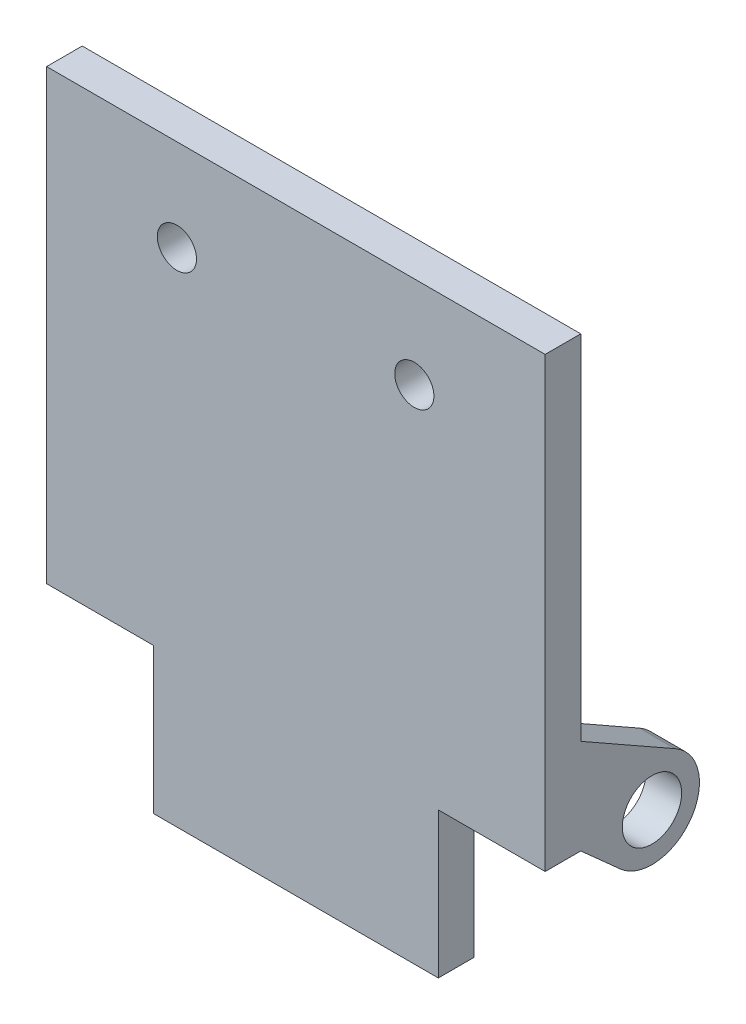
SolidWorks part; units mm, degrees
ref_plane "前视基准面" through (0, 0, 0) normal (0, 0, 1) x (1, 0, 0)
ref_plane "上视基准面" through (0, 0, 0) normal (0, 1, 0) x (1, 0, 0)
ref_plane "右视基准面" through (0, 0, 0) normal (1, 0, 0) x (0, 0, -1)
sketch "草图1" plane through (0, 0, 0) normal (0, 0, 1) x (1, 0, 0)
  line L1 (-21, 25) -> (21, 25)
  line L2 (-21, 25) -> (-21, -25)
  line L3 (-21, -25) -> (21, -25)
  line L4 (21, 25) -> (21, -25)
  line L5 (-21, 25) -> (21, -25) construction
  line L6 (-21, -25) -> (21, 25) construction
  point P0 (0, 0)
  dimension "D1" = 42
  dimension "D2" = 50
extrude "凸台-拉伸1" add sketch "草图1" along normal blind 3
sketch "草图3" plane through (0, 0, 0) normal (0, 0, -1) x (-1, 0, 0)
  line L0 (21, -25) -> (-21, -25) construction
  line L1 (5, -25) -> (2, -25)
  line L2 (5, -25) -> (5, -20)
  line L3 (5, -20) -> (2, -20)
  line L4 (2, -25) -> (2, -20)
  line L5 (21, 25) -> (21, -25) construction
  line L6 (5, 3) -> (2, 3)
  line L7 (5, 3) -> (5, 13)
  line L8 (5, 13) -> (2, 13)
  line L9 (2, 3) -> (2, 13)
  dimension "D1" = 16
  dimension "D2" = 5
  dimension "D3" = 23
  dimension "D4" = 10
  dimension "D5" = 3
extrude "凸台-拉伸2" add sketch "草图3" along normal blind 12
fillet "圆角1" radius 5 1 edges at (-2, 8, 0)
fillet "圆角2" radius 5 1 edges at (-2, -22.5, 0)
sketch "草图4" plane through (-5, 0, 0) normal (-1, 0, 0) x (0, 0, 1)
  line L0 (-12, -20) -> (0, -20) construction
  line L1 (-12, 3) -> (0, 3) construction
  circle A0 centre (-5.947, -22) radius 1
  circle A1 centre (-5.947, 5) radius 1
  dimension "D1" = 2
  dimension "D2" = 2
  dimension "D3" = 2
extrude "切除-拉伸1" cut sketch "草图4" against normal through all
sketch "草图5" plane through (21, 0, 0) normal (1, 0, 0) x (0, 0, -1)
  line L0 (0, -25) -> (0, 25) construction
  line L1 (0, -4.734) -> (0, -12.734)
  line L2 (0, -4.734) -> (7.9728, -9.2543)
  line L3 (0, -12.734) -> (3.3333, -15.7154)
  arc A0 (3.3333, -15.7154) -> (7.9728, -9.2543) centre (6, -12.734) ccw
  circle A1 centre (6, -12.734) radius 2.5
  dimension "D1" = 8
  dimension "D3" = 5
  dimension "D2" = 6
  dimension "D4" = 8
extrude "凸台-拉伸3" add sketch "草图5" against normal blind 3
sketch "草图6" plane through (0, 0, 0) normal (0, 0, -1) x (-1, 0, 0)
  line L0 (-21, -25) -> (-21, -12.734)
  line L1 (-21, -25) -> (-12, -25)
  line L2 (-21, -12.734) -> (-12, -12.734)
  line L3 (-12, -25) -> (-12, -12.734)
  line L4 (-21, -25) -> (-21, -12.734) construction
  line L6 (21, -25) -> (12, -25)
  line L7 (21, -25) -> (21, -12.734)
  line L8 (21, -12.734) -> (12, -12.734)
  line L9 (12, -25) -> (12, -12.734)
  dimension "D2" = 9
extrude "切除-拉伸2" cut sketch "草图6" against normal through all
sketch "草图7" plane through (0, 0, 3) normal (0, 0, 1) x (1, 0, 0)
  line L1 (-21, 17.266) -> (20.9516, 17.266) construction
  line L2 (-21, 25) -> (-21, -12.734) construction
  line L3 (12, -12.734) -> (21, -12.734) construction
  circle A0 centre (9.9758, 17.266) radius 1.65
  circle A1 centre (-10.0242, 17.266) radius 1.65
  point P2 (-0.0242, 17.266)
  point P11 (16.5, -12.734)
  dimension "D1" = 10
  dimension "D2" = 10
  dimension "D3" = 3.3
  dimension "D4" = 30
extrude "切除-拉伸3" cut sketch "草图7" against normal through all
fillet "圆角3" radius 3 1 edges at (-3.5, -25, -12)
